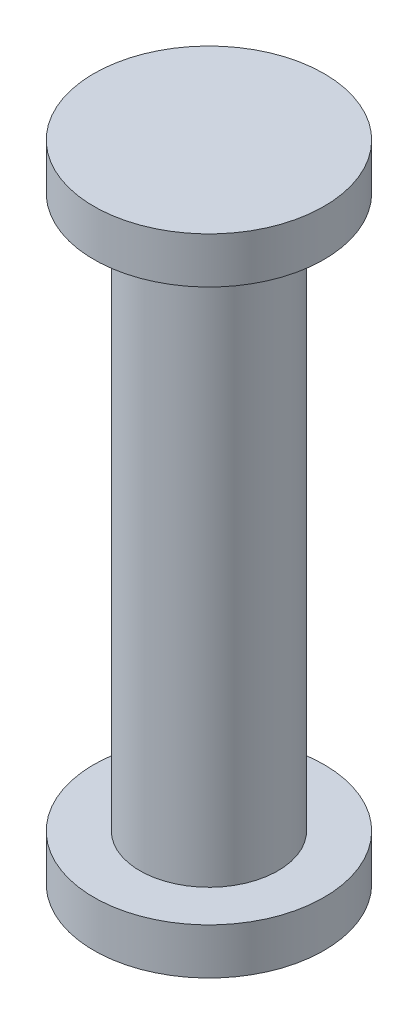
SolidWorks part; units mm, degrees
ref_plane "Front Plane" through (0, 0, 0) normal (0, 0, 1) x (1, 0, 0)
ref_plane "Top Plane" through (0, 0, 0) normal (0, 1, 0) x (1, 0, 0)
ref_plane "Right Plane" through (0, 0, 0) normal (1, 0, 0) x (0, 0, -1)
sketch "Sketch1" plane through (0, 0, 0) normal (0, 0, 1) x (1, 0, 0)
  line L0 (0, 0) -> (0, 14)
  line L1 (0, 14) -> (-2.5, 14)
  line L3 (-1.5, 1) -> (-2.5, 1)
  line L4 (-2.5, 1) -> (-2.5, 0)
  line L5 (-2.5, 0) -> (0, 0)
  line L6 (-2.5, 14) -> (-2.5, 13)
  line L7 (-2.5, 13) -> (-1.5, 13)
  line L8 (-1.5, 13) -> (-1.5, 1)
  point P5 (-3.2289, 2.616)
  dimension "D1" = 14
  dimension "D2" = 1
  dimension "D3" = 2.5
  dimension "D4" = 1.5
  dimension "D5" = 1
  dimension "D6" = 2.5
revolve "Revolve1" add sketch "Sketch1" angle 360 about L0
